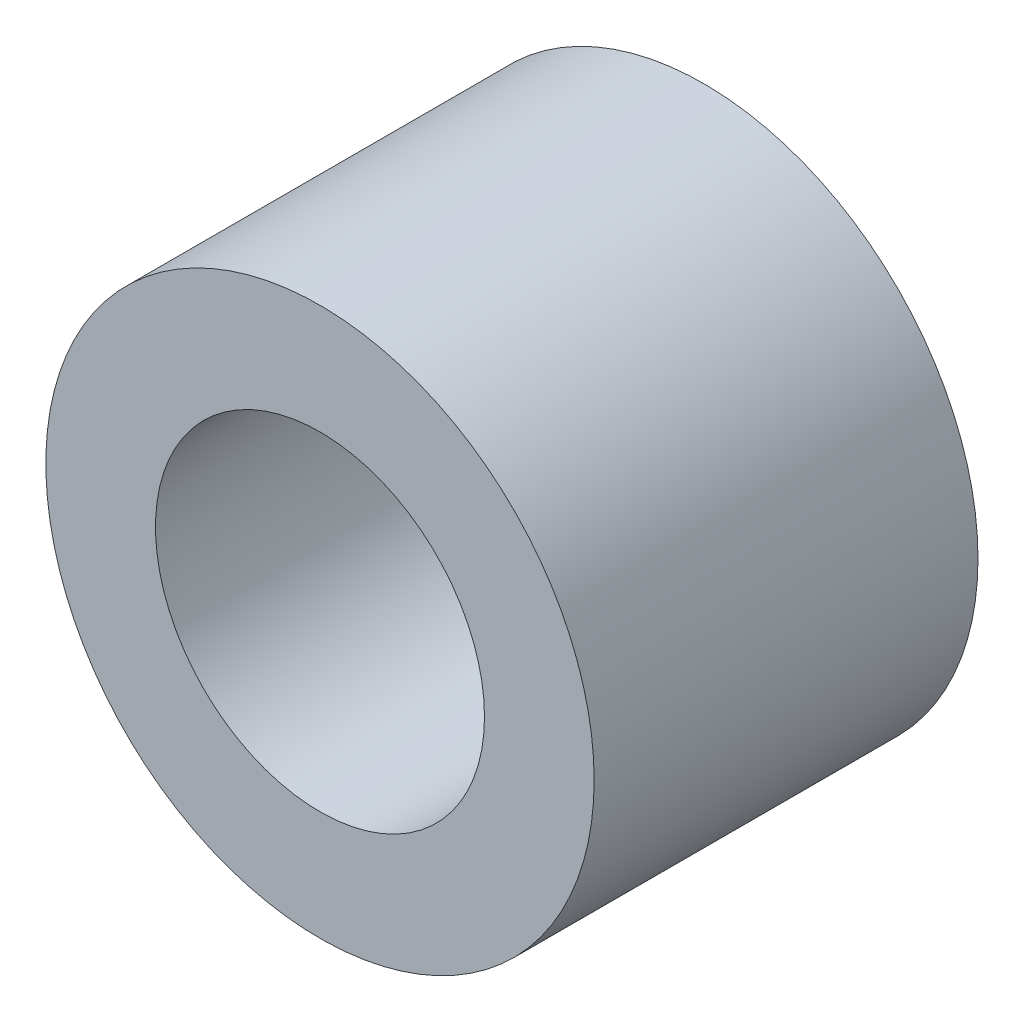
SolidWorks part; units mm, degrees
material "ﾎﾟﾘｵｷｼﾒﾁﾚﾝ(POM)ｱｾﾀｰﾙ共重合体"
ref_plane "Front Plane" through (0, 0, 0) normal (0, 0, 1) x (1, 0, 0)
ref_plane "Top Plane" through (0, 0, 0) normal (0, 1, 0) x (1, 0, 0)
ref_plane "Right Plane" through (0, 0, 0) normal (1, 0, 0) x (0, 0, -1)
sketch "Sketch2" plane through (0, 0, 0) normal (0, 0, 1) x (1, 0, 0)
  circle A0 centre (0, 0) radius 2.5
  circle A1 centre (0, 0) radius 1.5
  dimension "D1" = 3
  dimension "D2" = 5
  dimension "D3" = 5
extrude "Boss-Extrude1" add sketch "Sketch2" along normal blind 3.5
